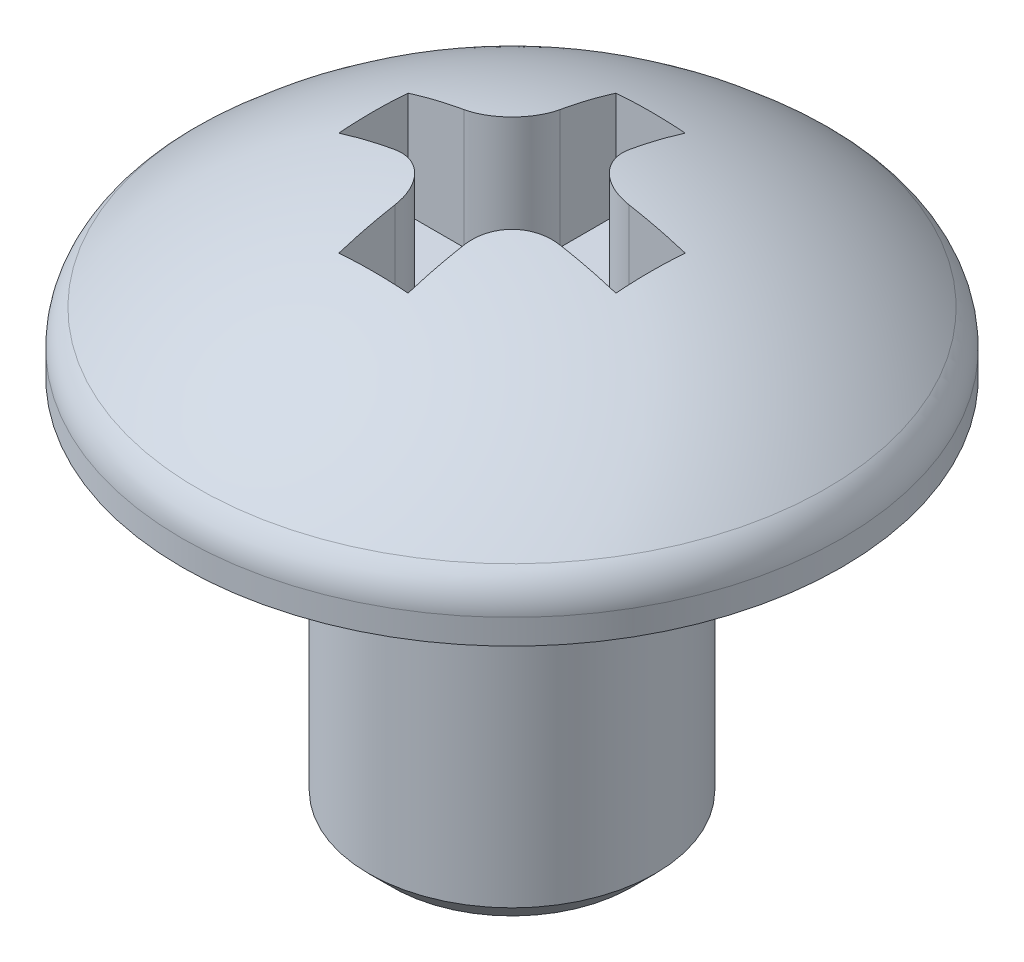
SolidWorks part; units mm, degrees
ref_plane "Front" through (0, 0, 0) normal (0, 0, 1) x (1, 0, 0)
ref_plane "Top" through (0, 0, 0) normal (0, 1, 0) x (1, 0, 0)
ref_plane "Right" through (0, 0, 0) normal (1, 0, 0) x (0, 0, -1)
sketch "Sketch1" plane through (0, 0, 0) normal (0, 0, 1) x (1, 0, 0)
  line L0 (0, -2.9888) -> (0, 4.5277) construction
  line L1 (0, -4) -> (1.5, -4)
  line L2 (1.5, -4) -> (1.5, 0)
  line L3 (1.5, 0) -> (3.45, 0)
  line L4 (3.45, 0) -> (3.45, 0.475)
  line L5 (0, 1.9) -> (0, -4)
  arc A0 (3.45, 0.475) -> (0, 1.9) centre (0, -2.9888) ccw
  dimension "d" = 3
  dimension "dk" = 6.9
  dimension "k" = 1.9
  dimension "l" = 4
  dimension "D1" = 0.475
revolve "Revolve1" add sketch "Sketch1" angle 360 about L0
ref_point "Point2"
ref_plane "Plane1" through (0, 1.9, 0) normal (0, 1, 0) x (-1, 0, 0)
sketch "Sketch3" plane through (0, 1.9, 0) normal (0, 1, 0) x (-1, 0, 0)
  line L0 (-0.3625, 1.45) -> (0.3625, 1.45)
  line L1 (0.3625, 1.45) -> (0.3625, 0.3625)
  line L2 (0.3625, 0.3625) -> (1.45, 0.3625)
  line L3 (1.45, 0.3625) -> (1.45, -0.3625)
  line L4 (1.45, -0.3625) -> (0.3625, -0.3625)
  line L5 (0.3625, -0.3625) -> (0.3625, -1.45)
  line L6 (0.3625, -1.45) -> (-0.3625, -1.45)
  line L7 (-0.3625, -1.45) -> (-0.3625, -0.3625)
  line L8 (-0.3625, -0.3625) -> (-1.45, -0.3625)
  line L9 (-1.45, -0.3625) -> (-1.45, 0.3625)
  line L10 (-1.45, 0.3625) -> (-0.3625, 0.3625)
  line L11 (-0.3625, 0.3625) -> (-0.3625, 1.45)
  line L12 (0, 1.2663) -> (0, -1.3215) construction
  line L13 (-1.2836, 0) -> (1.5044, 0) construction
  dimension "m" = 2.9
  dimension "D2" = 0.725
  dimension "D1" = 2.9
extrude "Cut-Extrude1" cut sketch "Sketch3" against normal blind 1.34
chamfer "Chamfer1" distance 0.25 angle 45 1 edges at (0, -4, -1.5)
fillet "Fillet1" radius 0.5 1 edges at (0, 0.475, -3.45)
fillet "Fillet2" radius 0.5 4 edges at (0.3625, 1.2165, -0.3625) (0.3625, 1.2165, 0.3625) (-0.3625, 1.2165, 0.3625) (-0.3625, 1.2165, -0.3625)
equation "\"D1@Sketch1\" = \"k@Sketch1\"/4"
equation "\"D2@Sketch3\" = \"m@Sketch3\"/4"
equation "\"D1@Fillet1\" = \"c@Chamfer1\"*2"
equation "\"D1@Sketch3\" = \"m@Sketch3\""
equation "\"D1@Fillet2\" = \"c@Chamfer1\"*2"
